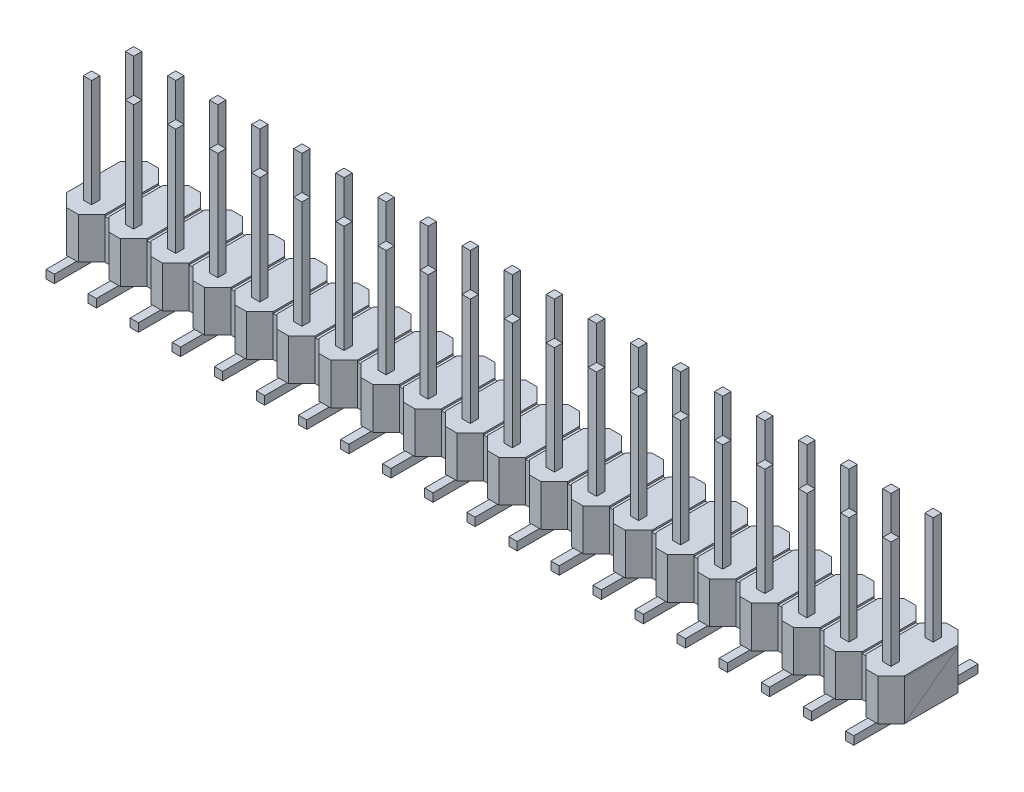
SolidWorks part; units mm, degrees
ref_plane "Alzado" through (0, 0, 0) normal (0, 0, 1) x (1, 0, 0)
ref_plane "Planta" through (0, 0, 0) normal (0, 1, 0) x (1, 0, 0)
ref_plane "Vista lateral" through (0, 0, 0) normal (1, 0, 0) x (0, 0, -1)
sketch "Croquis1" plane through (0, 0, 0) normal (0, 1, 0) x (1, 0, 0)
  line L0 (2.54, 0) -> (3.04, 0)
  line L1 (0, 0) -> (0.5, 0)
  line L2 (0, 0) -> (0, 0.5)
  line L3 (0, 0.5) -> (0.5, 0.5)
  line L4 (0.5, 0) -> (0.5, 0.5)
  line L5 (2.54, 0) -> (2.54, 0.5)
  line L6 (2.54, 0.5) -> (3.04, 0.5)
  line L7 (3.04, 0) -> (3.04, 0.5)
  line L8 (5.08, 0) -> (5.58, 0)
  line L9 (5.08, 0) -> (5.08, 0.5)
  line L10 (5.08, 0.5) -> (5.58, 0.5)
  line L11 (5.58, 0) -> (5.58, 0.5)
  line L12 (7.62, 0) -> (8.12, 0)
  line L13 (7.62, 0) -> (7.62, 0.5)
  line L14 (7.62, 0.5) -> (8.12, 0.5)
  line L15 (8.12, 0) -> (8.12, 0.5)
  line L16 (10.16, 0) -> (10.66, 0)
  line L17 (10.16, 0) -> (10.16, 0.5)
  line L18 (10.16, 0.5) -> (10.66, 0.5)
  line L19 (10.66, 0) -> (10.66, 0.5)
  line L20 (12.7, 0) -> (13.2, 0)
  line L21 (12.7, 0) -> (12.7, 0.5)
  line L22 (12.7, 0.5) -> (13.2, 0.5)
  line L23 (13.2, 0) -> (13.2, 0.5)
  line L24 (15.24, 0) -> (15.74, 0)
  line L25 (15.24, 0) -> (15.24, 0.5)
  line L26 (15.24, 0.5) -> (15.74, 0.5)
  line L27 (15.74, 0) -> (15.74, 0.5)
  line L28 (17.78, 0) -> (18.28, 0)
  line L29 (17.78, 0) -> (17.78, 0.5)
  line L30 (17.78, 0.5) -> (18.28, 0.5)
  line L31 (18.28, 0) -> (18.28, 0.5)
  line L32 (20.32, 0) -> (20.82, 0)
  line L33 (20.32, 0) -> (20.32, 0.5)
  line L34 (20.32, 0.5) -> (20.82, 0.5)
  line L35 (20.82, 0) -> (20.82, 0.5)
  line L36 (22.86, 0) -> (23.36, 0)
  line L37 (22.86, 0) -> (22.86, 0.5)
  line L38 (22.86, 0.5) -> (23.36, 0.5)
  line L39 (23.36, 0) -> (23.36, 0.5)
  line L40 (25.4, 0) -> (25.9, 0)
  line L41 (25.4, 0) -> (25.4, 0.5)
  line L42 (25.4, 0.5) -> (25.9, 0.5)
  line L43 (25.9, 0) -> (25.9, 0.5)
  line L44 (27.94, 0) -> (28.44, 0)
  line L45 (27.94, 0) -> (27.94, 0.5)
  line L46 (27.94, 0.5) -> (28.44, 0.5)
  line L47 (28.44, 0) -> (28.44, 0.5)
  line L48 (30.48, 0) -> (30.98, 0)
  line L49 (30.48, 0) -> (30.48, 0.5)
  line L50 (30.48, 0.5) -> (30.98, 0.5)
  line L51 (30.98, 0) -> (30.98, 0.5)
  line L52 (33.02, 0) -> (33.52, 0)
  line L53 (33.02, 0) -> (33.02, 0.5)
  line L54 (33.02, 0.5) -> (33.52, 0.5)
  line L55 (33.52, 0) -> (33.52, 0.5)
  line L56 (35.56, 0) -> (36.06, 0)
  line L57 (35.56, 0) -> (35.56, 0.5)
  line L58 (35.56, 0.5) -> (36.06, 0.5)
  line L59 (36.06, 0) -> (36.06, 0.5)
  line L60 (38.1, 0) -> (38.6, 0)
  line L61 (38.1, 0) -> (38.1, 0.5)
  line L62 (38.1, 0.5) -> (38.6, 0.5)
  line L63 (38.6, 0) -> (38.6, 0.5)
  line L64 (40.64, 0) -> (41.14, 0)
  line L65 (40.64, 0) -> (40.64, 0.5)
  line L66 (40.64, 0.5) -> (41.14, 0.5)
  line L67 (41.14, 0) -> (41.14, 0.5)
  line L68 (43.18, 0) -> (43.68, 0)
  line L69 (43.18, 0) -> (43.18, 0.5)
  line L70 (43.18, 0.5) -> (43.68, 0.5)
  line L71 (43.68, 0) -> (43.68, 0.5)
  line L72 (45.72, 0) -> (46.22, 0)
  line L73 (45.72, 0) -> (45.72, 0.5)
  line L74 (45.72, 0.5) -> (46.22, 0.5)
  line L75 (46.22, 0) -> (46.22, 0.5)
  line L76 (48.26, 0) -> (48.76, 0)
  line L77 (48.26, 0) -> (48.26, 0.5)
  line L78 (48.26, 0.5) -> (48.76, 0.5)
  line L79 (48.76, 0) -> (48.76, 0.5)
  line L80 (0, 2.54) -> (0.5, 2.54)
  line L81 (0, 2.54) -> (0, 3.04)
  line L82 (0, 3.04) -> (0.5, 3.04)
  line L83 (0.5, 2.54) -> (0.5, 3.04)
  line L84 (2.54, 2.54) -> (3.04, 2.54)
  line L85 (2.54, 2.54) -> (2.54, 3.04)
  line L86 (2.54, 3.04) -> (3.04, 3.04)
  line L87 (3.04, 2.54) -> (3.04, 3.04)
  line L88 (5.08, 2.54) -> (5.58, 2.54)
  line L89 (5.08, 2.54) -> (5.08, 3.04)
  line L90 (5.08, 3.04) -> (5.58, 3.04)
  line L91 (5.58, 2.54) -> (5.58, 3.04)
  line L92 (7.62, 2.54) -> (8.12, 2.54)
  line L93 (7.62, 2.54) -> (7.62, 3.04)
  line L94 (7.62, 3.04) -> (8.12, 3.04)
  line L95 (8.12, 2.54) -> (8.12, 3.04)
  line L96 (10.16, 2.54) -> (10.66, 2.54)
  line L97 (10.16, 2.54) -> (10.16, 3.04)
  line L98 (10.16, 3.04) -> (10.66, 3.04)
  line L99 (10.66, 2.54) -> (10.66, 3.04)
  line L100 (12.7, 2.54) -> (13.2, 2.54)
  line L101 (12.7, 2.54) -> (12.7, 3.04)
  line L102 (12.7, 3.04) -> (13.2, 3.04)
  line L103 (13.2, 2.54) -> (13.2, 3.04)
  line L104 (15.24, 2.54) -> (15.74, 2.54)
  line L105 (15.24, 2.54) -> (15.24, 3.04)
  line L106 (15.24, 3.04) -> (15.74, 3.04)
  line L107 (15.74, 2.54) -> (15.74, 3.04)
  line L108 (17.78, 2.54) -> (18.28, 2.54)
  line L109 (17.78, 2.54) -> (17.78, 3.04)
  line L110 (17.78, 3.04) -> (18.28, 3.04)
  line L111 (18.28, 2.54) -> (18.28, 3.04)
  line L112 (20.32, 2.54) -> (20.82, 2.54)
  line L113 (20.32, 2.54) -> (20.32, 3.04)
  line L114 (20.32, 3.04) -> (20.82, 3.04)
  line L115 (20.82, 2.54) -> (20.82, 3.04)
  line L116 (22.86, 2.54) -> (23.36, 2.54)
  line L117 (22.86, 2.54) -> (22.86, 3.04)
  line L118 (22.86, 3.04) -> (23.36, 3.04)
  line L119 (23.36, 2.54) -> (23.36, 3.04)
  line L120 (25.4, 2.54) -> (25.9, 2.54)
  line L121 (25.4, 2.54) -> (25.4, 3.04)
  line L122 (25.4, 3.04) -> (25.9, 3.04)
  line L123 (25.9, 2.54) -> (25.9, 3.04)
  line L124 (27.94, 2.54) -> (28.44, 2.54)
  line L125 (27.94, 2.54) -> (27.94, 3.04)
  line L126 (27.94, 3.04) -> (28.44, 3.04)
  line L127 (28.44, 2.54) -> (28.44, 3.04)
  line L128 (30.48, 2.54) -> (30.98, 2.54)
  line L129 (30.48, 2.54) -> (30.48, 3.04)
  line L130 (30.48, 3.04) -> (30.98, 3.04)
  line L131 (30.98, 2.54) -> (30.98, 3.04)
  line L132 (33.02, 2.54) -> (33.52, 2.54)
  line L133 (33.02, 2.54) -> (33.02, 3.04)
  line L134 (33.02, 3.04) -> (33.52, 3.04)
  line L135 (33.52, 2.54) -> (33.52, 3.04)
  line L136 (35.56, 2.54) -> (36.06, 2.54)
  line L137 (35.56, 2.54) -> (35.56, 3.04)
  line L138 (35.56, 3.04) -> (36.06, 3.04)
  line L139 (36.06, 2.54) -> (36.06, 3.04)
  line L140 (38.1, 2.54) -> (38.6, 2.54)
  line L141 (38.1, 2.54) -> (38.1, 3.04)
  line L142 (38.1, 3.04) -> (38.6, 3.04)
  line L143 (38.6, 2.54) -> (38.6, 3.04)
  line L144 (40.64, 2.54) -> (41.14, 2.54)
  line L145 (40.64, 2.54) -> (40.64, 3.04)
  line L146 (40.64, 3.04) -> (41.14, 3.04)
  line L147 (41.14, 2.54) -> (41.14, 3.04)
  line L148 (43.18, 2.54) -> (43.68, 2.54)
  line L149 (43.18, 2.54) -> (43.18, 3.04)
  line L150 (43.18, 3.04) -> (43.68, 3.04)
  line L151 (43.68, 2.54) -> (43.68, 3.04)
  line L152 (45.72, 2.54) -> (46.22, 2.54)
  line L153 (45.72, 2.54) -> (45.72, 3.04)
  line L154 (45.72, 3.04) -> (46.22, 3.04)
  line L155 (46.22, 2.54) -> (46.22, 3.04)
  line L156 (48.26, 2.54) -> (48.76, 2.54)
  line L157 (48.26, 2.54) -> (48.26, 3.04)
  line L158 (48.26, 3.04) -> (48.76, 3.04)
  line L159 (48.76, 2.54) -> (48.76, 3.04)
  line L160 (0, 0) -> (2.54, 0) construction
  line L161 (0, 0) -> (0, 2.54) construction
  dimension "D1" = 0.5
  dimension "D2" = 0.5
  dimension "D3" = 90
  dimension "D4" = 2.54
  dimension "D5" = 2.54
extrude "Extruir1" add sketch "Croquis1" along normal blind 9.5
sketch "Croquis2" plane through (0, 0, 0) normal (0, -1, 0) x (1, 0, 0)
  line L0 (2.54, 2.25) -> (3.04, 2.25)
  line L1 (0, 2.25) -> (0.5, 2.25)
  line L2 (0, 2.25) -> (0, -5.25)
  line L3 (0, -5.25) -> (0.5, -5.25)
  line L4 (0.5, 2.25) -> (0.5, -5.25)
  line L5 (2.54, 2.25) -> (2.54, -5.25)
  line L6 (2.54, -5.25) -> (3.04, -5.25)
  line L7 (3.04, 2.25) -> (3.04, -5.25)
  line L8 (5.08, 2.25) -> (5.58, 2.25)
  line L9 (5.08, 2.25) -> (5.08, -5.25)
  line L10 (5.08, -5.25) -> (5.58, -5.25)
  line L11 (5.58, 2.25) -> (5.58, -5.25)
  line L12 (7.62, 2.25) -> (8.12, 2.25)
  line L13 (7.62, 2.25) -> (7.62, -5.25)
  line L14 (7.62, -5.25) -> (8.12, -5.25)
  line L15 (8.12, 2.25) -> (8.12, -5.25)
  line L16 (10.16, 2.25) -> (10.66, 2.25)
  line L17 (10.16, 2.25) -> (10.16, -5.25)
  line L18 (10.16, -5.25) -> (10.66, -5.25)
  line L19 (10.66, 2.25) -> (10.66, -5.25)
  line L20 (12.7, 2.25) -> (13.2, 2.25)
  line L21 (12.7, 2.25) -> (12.7, -5.25)
  line L22 (12.7, -5.25) -> (13.2, -5.25)
  line L23 (13.2, 2.25) -> (13.2, -5.25)
  line L24 (15.24, 2.25) -> (15.74, 2.25)
  line L25 (15.24, 2.25) -> (15.24, -5.25)
  line L26 (15.24, -5.25) -> (15.74, -5.25)
  line L27 (15.74, 2.25) -> (15.74, -5.25)
  line L28 (17.78, 2.25) -> (18.28, 2.25)
  line L29 (17.78, 2.25) -> (17.78, -5.25)
  line L30 (17.78, -5.25) -> (18.28, -5.25)
  line L31 (18.28, 2.25) -> (18.28, -5.25)
  line L32 (20.32, 2.25) -> (20.82, 2.25)
  line L33 (20.32, 2.25) -> (20.32, -5.25)
  line L34 (20.32, -5.25) -> (20.82, -5.25)
  line L35 (20.82, 2.25) -> (20.82, -5.25)
  line L36 (22.86, 2.25) -> (23.36, 2.25)
  line L37 (22.86, 2.25) -> (22.86, -5.25)
  line L38 (22.86, -5.25) -> (23.36, -5.25)
  line L39 (23.36, 2.25) -> (23.36, -5.25)
  line L40 (25.4, 2.25) -> (25.9, 2.25)
  line L41 (25.4, 2.25) -> (25.4, -5.25)
  line L42 (25.4, -5.25) -> (25.9, -5.25)
  line L43 (25.9, 2.25) -> (25.9, -5.25)
  line L44 (27.94, 2.25) -> (28.44, 2.25)
  line L45 (27.94, 2.25) -> (27.94, -5.25)
  line L46 (27.94, -5.25) -> (28.44, -5.25)
  line L47 (28.44, 2.25) -> (28.44, -5.25)
  line L48 (30.48, 2.25) -> (30.98, 2.25)
  line L49 (30.48, 2.25) -> (30.48, -5.25)
  line L50 (30.48, -5.25) -> (30.98, -5.25)
  line L51 (30.98, 2.25) -> (30.98, -5.25)
  line L52 (33.02, 2.25) -> (33.52, 2.25)
  line L53 (33.02, 2.25) -> (33.02, -5.25)
  line L54 (33.02, -5.25) -> (33.52, -5.25)
  line L55 (33.52, 2.25) -> (33.52, -5.25)
  line L56 (35.56, 2.25) -> (36.06, 2.25)
  line L57 (35.56, 2.25) -> (35.56, -5.25)
  line L58 (35.56, -5.25) -> (36.06, -5.25)
  line L59 (36.06, 2.25) -> (36.06, -5.25)
  line L60 (38.1, 2.25) -> (38.6, 2.25)
  line L61 (38.1, 2.25) -> (38.1, -5.25)
  line L62 (38.1, -5.25) -> (38.6, -5.25)
  line L63 (38.6, 2.25) -> (38.6, -5.25)
  line L64 (40.64, 2.25) -> (41.14, 2.25)
  line L65 (40.64, 2.25) -> (40.64, -5.25)
  line L66 (40.64, -5.25) -> (41.14, -5.25)
  line L67 (41.14, 2.25) -> (41.14, -5.25)
  line L68 (43.18, 2.25) -> (43.68, 2.25)
  line L69 (43.18, 2.25) -> (43.18, -5.25)
  line L70 (43.18, -5.25) -> (43.68, -5.25)
  line L71 (43.68, 2.25) -> (43.68, -5.25)
  line L72 (45.72, 2.25) -> (46.22, 2.25)
  line L73 (45.72, 2.25) -> (45.72, -5.25)
  line L74 (45.72, -5.25) -> (46.22, -5.25)
  line L75 (46.22, 2.25) -> (46.22, -5.25)
  line L76 (48.26, 2.25) -> (48.76, 2.25)
  line L77 (48.26, 2.25) -> (48.26, -5.25)
  line L78 (48.26, -5.25) -> (48.76, -5.25)
  line L79 (48.76, 2.25) -> (48.76, -5.25)
  dimension "D1" = 7.5
  dimension "D2" = 0.5
  dimension "D3" = 2.25
  dimension "D4" = 2.54
extrude "Extruir2" add sketch "Croquis2" against normal blind 0.5
sketch "Croquis3" plane through (0, 0.5, 0) normal (0, 1, 0) x (-1, 0, 0)
  line L0 (-0.5, -5.25) -> (-0.5, -3.04) construction
  line L1 (-0.6, -3.94) -> (0.1, -3.94)
  line L2 (-1.4, -3.14) -> (-1.4, 0.1)
  line L3 (-0.6, 0.9) -> (0.1, 0.9)
  line L4 (0.9, -3.14) -> (0.9, 0.1)
  line L5 (0, -3.04) -> (0, -5.25) construction
  line L6 (-0.5, -3.04) -> (0, -3.04) construction
  line L7 (-0.5, 0) -> (0, 0) construction
  line L8 (-1.4, -3.14) -> (-0.6, -3.94)
  line L9 (0.1, -3.94) -> (0.9, -3.14)
  line L10 (0.1, 0.9) -> (0.9, 0.1)
  line L11 (-1.4, 0.1) -> (-0.6, 0.9)
  line L12 (-3.14, -3.94) -> (-2.44, -3.94)
  line L13 (-3.94, -3.14) -> (-3.94, 0.1)
  line L14 (-3.14, 0.9) -> (-2.44, 0.9)
  line L15 (-1.64, -3.14) -> (-1.64, 0.1)
  line L16 (-3.94, -3.14) -> (-3.14, -3.94)
  line L17 (-2.44, -3.94) -> (-1.64, -3.14)
  line L18 (-2.44, 0.9) -> (-1.64, 0.1)
  line L19 (-3.94, 0.1) -> (-3.14, 0.9)
  line L20 (-5.68, -3.94) -> (-4.98, -3.94)
  line L21 (-6.48, -3.14) -> (-6.48, 0.1)
  line L22 (-5.68, 0.9) -> (-4.98, 0.9)
  line L23 (-4.18, -3.14) -> (-4.18, 0.1)
  line L24 (-6.48, -3.14) -> (-5.68, -3.94)
  line L25 (-4.98, -3.94) -> (-4.18, -3.14)
  line L26 (-4.98, 0.9) -> (-4.18, 0.1)
  line L27 (-6.48, 0.1) -> (-5.68, 0.9)
  line L28 (-8.22, -3.94) -> (-7.52, -3.94)
  line L29 (-9.02, -3.14) -> (-9.02, 0.1)
  line L30 (-8.22, 0.9) -> (-7.52, 0.9)
  line L31 (-6.72, -3.14) -> (-6.72, 0.1)
  line L32 (-9.02, -3.14) -> (-8.22, -3.94)
  line L33 (-7.52, -3.94) -> (-6.72, -3.14)
  line L34 (-7.52, 0.9) -> (-6.72, 0.1)
  line L35 (-9.02, 0.1) -> (-8.22, 0.9)
  line L36 (-10.76, -3.94) -> (-10.06, -3.94)
  line L37 (-11.56, -3.14) -> (-11.56, 0.1)
  line L38 (-10.76, 0.9) -> (-10.06, 0.9)
  line L39 (-9.26, -3.14) -> (-9.26, 0.1)
  line L40 (-11.56, -3.14) -> (-10.76, -3.94)
  line L41 (-10.06, -3.94) -> (-9.26, -3.14)
  line L42 (-10.06, 0.9) -> (-9.26, 0.1)
  line L43 (-11.56, 0.1) -> (-10.76, 0.9)
  line L44 (-13.3, -3.94) -> (-12.6, -3.94)
  line L45 (-14.1, -3.14) -> (-14.1, 0.1)
  line L46 (-13.3, 0.9) -> (-12.6, 0.9)
  line L47 (-11.8, -3.14) -> (-11.8, 0.1)
  line L48 (-14.1, -3.14) -> (-13.3, -3.94)
  line L49 (-12.6, -3.94) -> (-11.8, -3.14)
  line L50 (-12.6, 0.9) -> (-11.8, 0.1)
  line L51 (-14.1, 0.1) -> (-13.3, 0.9)
  line L52 (-15.84, -3.94) -> (-15.14, -3.94)
  line L53 (-16.64, -3.14) -> (-16.64, 0.1)
  line L54 (-15.84, 0.9) -> (-15.14, 0.9)
  line L55 (-14.34, -3.14) -> (-14.34, 0.1)
  line L56 (-16.64, -3.14) -> (-15.84, -3.94)
  line L57 (-15.14, -3.94) -> (-14.34, -3.14)
  line L58 (-15.14, 0.9) -> (-14.34, 0.1)
  line L59 (-16.64, 0.1) -> (-15.84, 0.9)
  line L60 (-18.38, -3.94) -> (-17.68, -3.94)
  line L61 (-19.18, -3.14) -> (-19.18, 0.1)
  line L62 (-18.38, 0.9) -> (-17.68, 0.9)
  line L63 (-16.88, -3.14) -> (-16.88, 0.1)
  line L64 (-19.18, -3.14) -> (-18.38, -3.94)
  line L65 (-17.68, -3.94) -> (-16.88, -3.14)
  line L66 (-17.68, 0.9) -> (-16.88, 0.1)
  line L67 (-19.18, 0.1) -> (-18.38, 0.9)
  line L68 (-20.92, -3.94) -> (-20.22, -3.94)
  line L69 (-21.72, -3.14) -> (-21.72, 0.1)
  line L70 (-20.92, 0.9) -> (-20.22, 0.9)
  line L71 (-19.42, -3.14) -> (-19.42, 0.1)
  line L72 (-21.72, -3.14) -> (-20.92, -3.94)
  line L73 (-20.22, -3.94) -> (-19.42, -3.14)
  line L74 (-20.22, 0.9) -> (-19.42, 0.1)
  line L75 (-21.72, 0.1) -> (-20.92, 0.9)
  line L76 (-23.46, -3.94) -> (-22.76, -3.94)
  line L77 (-24.26, -3.14) -> (-24.26, 0.1)
  line L78 (-23.46, 0.9) -> (-22.76, 0.9)
  line L79 (-21.96, -3.14) -> (-21.96, 0.1)
  line L80 (-24.26, -3.14) -> (-23.46, -3.94)
  line L81 (-22.76, -3.94) -> (-21.96, -3.14)
  line L82 (-22.76, 0.9) -> (-21.96, 0.1)
  line L83 (-24.26, 0.1) -> (-23.46, 0.9)
  line L84 (-26, -3.94) -> (-25.3, -3.94)
  line L85 (-26.8, -3.14) -> (-26.8, 0.1)
  line L86 (-26, 0.9) -> (-25.3, 0.9)
  line L87 (-24.5, -3.14) -> (-24.5, 0.1)
  line L88 (-26.8, -3.14) -> (-26, -3.94)
  line L89 (-25.3, -3.94) -> (-24.5, -3.14)
  line L90 (-25.3, 0.9) -> (-24.5, 0.1)
  line L91 (-26.8, 0.1) -> (-26, 0.9)
  line L92 (-28.54, -3.94) -> (-27.84, -3.94)
  line L93 (-29.34, -3.14) -> (-29.34, 0.1)
  line L94 (-28.54, 0.9) -> (-27.84, 0.9)
  line L95 (-27.04, -3.14) -> (-27.04, 0.1)
  line L96 (-29.34, -3.14) -> (-28.54, -3.94)
  line L97 (-27.84, -3.94) -> (-27.04, -3.14)
  line L98 (-27.84, 0.9) -> (-27.04, 0.1)
  line L99 (-29.34, 0.1) -> (-28.54, 0.9)
  line L100 (-31.08, -3.94) -> (-30.38, -3.94)
  line L101 (-31.88, -3.14) -> (-31.88, 0.1)
  line L102 (-31.08, 0.9) -> (-30.38, 0.9)
  line L103 (-29.58, -3.14) -> (-29.58, 0.1)
  line L104 (-31.88, -3.14) -> (-31.08, -3.94)
  line L105 (-30.38, -3.94) -> (-29.58, -3.14)
  line L106 (-30.38, 0.9) -> (-29.58, 0.1)
  line L107 (-31.88, 0.1) -> (-31.08, 0.9)
  line L108 (-33.62, -3.94) -> (-32.92, -3.94)
  line L109 (-34.42, -3.14) -> (-34.42, 0.1)
  line L110 (-33.62, 0.9) -> (-32.92, 0.9)
  line L111 (-32.12, -3.14) -> (-32.12, 0.1)
  line L112 (-34.42, -3.14) -> (-33.62, -3.94)
  line L113 (-32.92, -3.94) -> (-32.12, -3.14)
  line L114 (-32.92, 0.9) -> (-32.12, 0.1)
  line L115 (-34.42, 0.1) -> (-33.62, 0.9)
  line L116 (-36.16, -3.94) -> (-35.46, -3.94)
  line L117 (-36.96, -3.14) -> (-36.96, 0.1)
  line L118 (-36.16, 0.9) -> (-35.46, 0.9)
  line L119 (-34.66, -3.14) -> (-34.66, 0.1)
  line L120 (-36.96, -3.14) -> (-36.16, -3.94)
  line L121 (-35.46, -3.94) -> (-34.66, -3.14)
  line L122 (-35.46, 0.9) -> (-34.66, 0.1)
  line L123 (-36.96, 0.1) -> (-36.16, 0.9)
  line L124 (-38.7, -3.94) -> (-38, -3.94)
  line L125 (-39.5, -3.14) -> (-39.5, 0.1)
  line L126 (-38.7, 0.9) -> (-38, 0.9)
  line L127 (-37.2, -3.14) -> (-37.2, 0.1)
  line L128 (-39.5, -3.14) -> (-38.7, -3.94)
  line L129 (-38, -3.94) -> (-37.2, -3.14)
  line L130 (-38, 0.9) -> (-37.2, 0.1)
  line L131 (-39.5, 0.1) -> (-38.7, 0.9)
  line L132 (-41.24, -3.94) -> (-40.54, -3.94)
  line L133 (-42.04, -3.14) -> (-42.04, 0.1)
  line L134 (-41.24, 0.9) -> (-40.54, 0.9)
  line L135 (-39.74, -3.14) -> (-39.74, 0.1)
  line L136 (-42.04, -3.14) -> (-41.24, -3.94)
  line L137 (-40.54, -3.94) -> (-39.74, -3.14)
  line L138 (-40.54, 0.9) -> (-39.74, 0.1)
  line L139 (-42.04, 0.1) -> (-41.24, 0.9)
  line L140 (-43.78, -3.94) -> (-43.08, -3.94)
  line L141 (-44.58, -3.14) -> (-44.58, 0.1)
  line L142 (-43.78, 0.9) -> (-43.08, 0.9)
  line L143 (-42.28, -3.14) -> (-42.28, 0.1)
  line L144 (-44.58, -3.14) -> (-43.78, -3.94)
  line L145 (-43.08, -3.94) -> (-42.28, -3.14)
  line L146 (-43.08, 0.9) -> (-42.28, 0.1)
  line L147 (-44.58, 0.1) -> (-43.78, 0.9)
  line L148 (-46.32, -3.94) -> (-45.62, -3.94)
  line L149 (-47.12, -3.14) -> (-47.12, 0.1)
  line L150 (-46.32, 0.9) -> (-45.62, 0.9)
  line L151 (-44.82, -3.14) -> (-44.82, 0.1)
  line L152 (-47.12, -3.14) -> (-46.32, -3.94)
  line L153 (-45.62, -3.94) -> (-44.82, -3.14)
  line L154 (-45.62, 0.9) -> (-44.82, 0.1)
  line L155 (-47.12, 0.1) -> (-46.32, 0.9)
  line L156 (-48.86, -3.94) -> (-48.16, -3.94)
  line L157 (-49.66, -3.14) -> (-49.66, 0.1)
  line L158 (-48.86, 0.9) -> (-48.16, 0.9)
  line L159 (-47.36, -3.14) -> (-47.36, 0.1)
  line L160 (-49.66, -3.14) -> (-48.86, -3.94)
  line L161 (-48.16, -3.94) -> (-47.36, -3.14)
  line L162 (-48.16, 0.9) -> (-47.36, 0.1)
  line L163 (-49.66, 0.1) -> (-48.86, 0.9)
  line L164 (-3.04, -3.04) -> (-2.54, -3.04)
  line L165 (-0.5, -3.04) -> (0, -3.04)
  line L166 (-0.5, -3.04) -> (-0.5, -2.54)
  line L167 (-0.5, -2.54) -> (0, -2.54)
  line L168 (0, -3.04) -> (0, -2.54)
  line L169 (-0.5, -0.5) -> (0, -0.5)
  line L170 (-0.5, -0.5) -> (-0.5, 0)
  line L171 (-0.5, 0) -> (0, 0)
  line L172 (0, -0.5) -> (0, 0)
  line L173 (-3.04, -3.04) -> (-3.04, -2.54)
  line L174 (-3.04, -2.54) -> (-2.54, -2.54)
  line L175 (-2.54, -3.04) -> (-2.54, -2.54)
  line L176 (-3.04, -0.5) -> (-2.54, -0.5)
  line L177 (-3.04, -0.5) -> (-3.04, 0)
  line L178 (-3.04, 0) -> (-2.54, 0)
  line L179 (-2.54, -0.5) -> (-2.54, 0)
  line L180 (-5.58, -3.04) -> (-5.08, -3.04)
  line L181 (-5.58, -3.04) -> (-5.58, -2.54)
  line L182 (-5.58, -2.54) -> (-5.08, -2.54)
  line L183 (-5.08, -3.04) -> (-5.08, -2.54)
  line L184 (-5.58, -0.5) -> (-5.08, -0.5)
  line L185 (-5.58, -0.5) -> (-5.58, 0)
  line L186 (-5.58, 0) -> (-5.08, 0)
  line L187 (-5.08, -0.5) -> (-5.08, 0)
  line L188 (-8.12, -3.04) -> (-7.62, -3.04)
  line L189 (-8.12, -3.04) -> (-8.12, -2.54)
  line L190 (-8.12, -2.54) -> (-7.62, -2.54)
  line L191 (-7.62, -3.04) -> (-7.62, -2.54)
  line L192 (-8.12, -0.5) -> (-7.62, -0.5)
  line L193 (-8.12, -0.5) -> (-8.12, 0)
  line L194 (-8.12, 0) -> (-7.62, 0)
  line L195 (-7.62, -0.5) -> (-7.62, 0)
  line L196 (-10.66, -3.04) -> (-10.16, -3.04)
  line L197 (-10.66, -3.04) -> (-10.66, -2.54)
  line L198 (-10.66, -2.54) -> (-10.16, -2.54)
  line L199 (-10.16, -3.04) -> (-10.16, -2.54)
  line L200 (-10.66, -0.5) -> (-10.16, -0.5)
  line L201 (-10.66, -0.5) -> (-10.66, 0)
  line L202 (-10.66, 0) -> (-10.16, 0)
  line L203 (-10.16, -0.5) -> (-10.16, 0)
  line L204 (-13.2, -3.04) -> (-12.7, -3.04)
  line L205 (-13.2, -3.04) -> (-13.2, -2.54)
  line L206 (-13.2, -2.54) -> (-12.7, -2.54)
  line L207 (-12.7, -3.04) -> (-12.7, -2.54)
  line L208 (-13.2, -0.5) -> (-12.7, -0.5)
  line L209 (-13.2, -0.5) -> (-13.2, 0)
  line L210 (-13.2, 0) -> (-12.7, 0)
  line L211 (-12.7, -0.5) -> (-12.7, 0)
  line L212 (-15.74, -3.04) -> (-15.24, -3.04)
  line L213 (-15.74, -3.04) -> (-15.74, -2.54)
  line L214 (-15.74, -2.54) -> (-15.24, -2.54)
  line L215 (-15.24, -3.04) -> (-15.24, -2.54)
  line L216 (-15.74, -0.5) -> (-15.24, -0.5)
  line L217 (-15.74, -0.5) -> (-15.74, 0)
  line L218 (-15.74, 0) -> (-15.24, 0)
  line L219 (-15.24, -0.5) -> (-15.24, 0)
  line L220 (-18.28, -3.04) -> (-17.78, -3.04)
  line L221 (-18.28, -3.04) -> (-18.28, -2.54)
  line L222 (-18.28, -2.54) -> (-17.78, -2.54)
  line L223 (-17.78, -3.04) -> (-17.78, -2.54)
  line L224 (-18.28, -0.5) -> (-17.78, -0.5)
  line L225 (-18.28, -0.5) -> (-18.28, 0)
  line L226 (-18.28, 0) -> (-17.78, 0)
  line L227 (-17.78, -0.5) -> (-17.78, 0)
  line L228 (-20.82, -3.04) -> (-20.32, -3.04)
  line L229 (-20.82, -3.04) -> (-20.82, -2.54)
  line L230 (-20.82, -2.54) -> (-20.32, -2.54)
  line L231 (-20.32, -3.04) -> (-20.32, -2.54)
  line L232 (-20.82, -0.5) -> (-20.32, -0.5)
  line L233 (-20.82, -0.5) -> (-20.82, 0)
  line L234 (-20.82, 0) -> (-20.32, 0)
  line L235 (-20.32, -0.5) -> (-20.32, 0)
  line L236 (-23.36, -3.04) -> (-22.86, -3.04)
  line L237 (-23.36, -3.04) -> (-23.36, -2.54)
  line L238 (-23.36, -2.54) -> (-22.86, -2.54)
  line L239 (-22.86, -3.04) -> (-22.86, -2.54)
  line L240 (-23.36, -0.5) -> (-22.86, -0.5)
  line L241 (-23.36, -0.5) -> (-23.36, 0)
  line L242 (-23.36, 0) -> (-22.86, 0)
  line L243 (-22.86, -0.5) -> (-22.86, 0)
  line L244 (-25.9, -3.04) -> (-25.4, -3.04)
  line L245 (-25.9, -3.04) -> (-25.9, -2.54)
  line L246 (-25.9, -2.54) -> (-25.4, -2.54)
  line L247 (-25.4, -3.04) -> (-25.4, -2.54)
  line L248 (-25.9, -0.5) -> (-25.4, -0.5)
  line L249 (-25.9, -0.5) -> (-25.9, 0)
  line L250 (-25.9, 0) -> (-25.4, 0)
  line L251 (-25.4, -0.5) -> (-25.4, 0)
  line L252 (-28.44, -3.04) -> (-27.94, -3.04)
  line L253 (-28.44, -3.04) -> (-28.44, -2.54)
  line L254 (-28.44, -2.54) -> (-27.94, -2.54)
  line L255 (-27.94, -3.04) -> (-27.94, -2.54)
  line L256 (-28.44, -0.5) -> (-27.94, -0.5)
  line L257 (-28.44, -0.5) -> (-28.44, 0)
  line L258 (-28.44, 0) -> (-27.94, 0)
  line L259 (-27.94, -0.5) -> (-27.94, 0)
  line L260 (-30.98, -3.04) -> (-30.48, -3.04)
  line L261 (-30.98, -3.04) -> (-30.98, -2.54)
  line L262 (-30.98, -2.54) -> (-30.48, -2.54)
  line L263 (-30.48, -3.04) -> (-30.48, -2.54)
  line L264 (-30.98, -0.5) -> (-30.48, -0.5)
  line L265 (-30.98, -0.5) -> (-30.98, 0)
  line L266 (-30.98, 0) -> (-30.48, 0)
  line L267 (-30.48, -0.5) -> (-30.48, 0)
  line L268 (-33.52, -3.04) -> (-33.02, -3.04)
  line L269 (-33.52, -3.04) -> (-33.52, -2.54)
  line L270 (-33.52, -2.54) -> (-33.02, -2.54)
  line L271 (-33.02, -3.04) -> (-33.02, -2.54)
  line L272 (-33.52, -0.5) -> (-33.02, -0.5)
  line L273 (-33.52, -0.5) -> (-33.52, 0)
  line L274 (-33.52, 0) -> (-33.02, 0)
  line L275 (-33.02, -0.5) -> (-33.02, 0)
  line L276 (-36.06, -3.04) -> (-35.56, -3.04)
  line L277 (-36.06, -3.04) -> (-36.06, -2.54)
  line L278 (-36.06, -2.54) -> (-35.56, -2.54)
  line L279 (-35.56, -3.04) -> (-35.56, -2.54)
  line L280 (-36.06, -0.5) -> (-35.56, -0.5)
  line L281 (-36.06, -0.5) -> (-36.06, 0)
  line L282 (-36.06, 0) -> (-35.56, 0)
  line L283 (-35.56, -0.5) -> (-35.56, 0)
  line L284 (-38.6, -3.04) -> (-38.1, -3.04)
  line L285 (-38.6, -3.04) -> (-38.6, -2.54)
  line L286 (-38.6, -2.54) -> (-38.1, -2.54)
  line L287 (-38.1, -3.04) -> (-38.1, -2.54)
  line L288 (-38.6, -0.5) -> (-38.1, -0.5)
  line L289 (-38.6, -0.5) -> (-38.6, 0)
  line L290 (-38.6, 0) -> (-38.1, 0)
  line L291 (-38.1, -0.5) -> (-38.1, 0)
  line L292 (-41.14, -3.04) -> (-40.64, -3.04)
  line L293 (-41.14, -3.04) -> (-41.14, -2.54)
  line L294 (-41.14, -2.54) -> (-40.64, -2.54)
  line L295 (-40.64, -3.04) -> (-40.64, -2.54)
  line L296 (-41.14, -0.5) -> (-40.64, -0.5)
  line L297 (-41.14, -0.5) -> (-41.14, 0)
  line L298 (-41.14, 0) -> (-40.64, 0)
  line L299 (-40.64, -0.5) -> (-40.64, 0)
  line L300 (-43.68, -3.04) -> (-43.18, -3.04)
  line L301 (-43.68, -3.04) -> (-43.68, -2.54)
  line L302 (-43.68, -2.54) -> (-43.18, -2.54)
  line L303 (-43.18, -3.04) -> (-43.18, -2.54)
  line L304 (-43.68, -0.5) -> (-43.18, -0.5)
  line L305 (-43.68, -0.5) -> (-43.68, 0)
  line L306 (-43.68, 0) -> (-43.18, 0)
  line L307 (-43.18, -0.5) -> (-43.18, 0)
  line L308 (-46.22, -3.04) -> (-45.72, -3.04)
  line L309 (-46.22, -3.04) -> (-46.22, -2.54)
  line L310 (-46.22, -2.54) -> (-45.72, -2.54)
  line L311 (-45.72, -3.04) -> (-45.72, -2.54)
  line L312 (-46.22, -0.5) -> (-45.72, -0.5)
  line L313 (-46.22, -0.5) -> (-46.22, 0)
  line L314 (-46.22, 0) -> (-45.72, 0)
  line L315 (-45.72, -0.5) -> (-45.72, 0)
  line L316 (-48.76, -3.04) -> (-48.26, -3.04)
  line L317 (-48.76, -3.04) -> (-48.76, -2.54)
  line L318 (-48.76, -2.54) -> (-48.26, -2.54)
  line L319 (-48.26, -3.04) -> (-48.26, -2.54)
  line L320 (-48.76, -0.5) -> (-48.26, -0.5)
  line L321 (-48.76, -0.5) -> (-48.76, 0)
  line L322 (-48.76, 0) -> (-48.26, 0)
  line L323 (-48.26, -0.5) -> (-48.26, 0)
  point P10 (-0.25, 0)
  point P15 (-1.4, -3.94)
  point P17 (0.9, -3.94)
  point P19 (0.9, 0.9)
  point P21 (-1.4, 0.9)
  point P27 (-3.94, 0.9)
  point P29 (-1.64, 0.9)
  point P31 (-1.64, -3.94)
  point P33 (-3.94, -3.94)
  point P39 (-6.48, 0.9)
  point P41 (-4.18, 0.9)
  point P43 (-4.18, -3.94)
  point P45 (-6.48, -3.94)
  point P51 (-9.02, 0.9)
  point P53 (-6.72, 0.9)
  point P55 (-6.72, -3.94)
  point P57 (-9.02, -3.94)
  point P63 (-11.56, 0.9)
  point P65 (-9.26, 0.9)
  point P67 (-9.26, -3.94)
  point P69 (-11.56, -3.94)
  point P75 (-14.1, 0.9)
  point P77 (-11.8, 0.9)
  point P79 (-11.8, -3.94)
  point P81 (-14.1, -3.94)
  point P87 (-16.64, 0.9)
  point P89 (-14.34, 0.9)
  point P91 (-14.34, -3.94)
  point P93 (-16.64, -3.94)
  point P99 (-19.18, 0.9)
  point P101 (-16.88, 0.9)
  point P103 (-16.88, -3.94)
  point P105 (-19.18, -3.94)
  point P111 (-21.72, 0.9)
  point P113 (-19.42, 0.9)
  point P115 (-19.42, -3.94)
  point P117 (-21.72, -3.94)
  point P123 (-24.26, 0.9)
  point P125 (-21.96, 0.9)
  point P127 (-21.96, -3.94)
  point P129 (-24.26, -3.94)
  point P135 (-26.8, 0.9)
  point P137 (-24.5, 0.9)
  point P139 (-24.5, -3.94)
  point P141 (-26.8, -3.94)
  point P147 (-29.34, 0.9)
  point P149 (-27.04, 0.9)
  point P151 (-27.04, -3.94)
  point P153 (-29.34, -3.94)
  point P159 (-31.88, 0.9)
  point P161 (-29.58, 0.9)
  point P163 (-29.58, -3.94)
  point P165 (-31.88, -3.94)
  point P171 (-34.42, 0.9)
  point P173 (-32.12, 0.9)
  point P175 (-32.12, -3.94)
  point P177 (-34.42, -3.94)
  point P183 (-36.96, 0.9)
  point P185 (-34.66, 0.9)
  point P187 (-34.66, -3.94)
  point P189 (-36.96, -3.94)
  point P195 (-39.5, 0.9)
  point P197 (-37.2, 0.9)
  point P199 (-37.2, -3.94)
  point P201 (-39.5, -3.94)
  point P207 (-42.04, 0.9)
  point P209 (-39.74, 0.9)
  point P211 (-39.74, -3.94)
  point P213 (-42.04, -3.94)
  point P219 (-44.58, 0.9)
  point P221 (-42.28, 0.9)
  point P223 (-42.28, -3.94)
  point P225 (-44.58, -3.94)
  point P231 (-47.12, 0.9)
  point P233 (-44.82, 0.9)
  point P235 (-44.82, -3.94)
  point P237 (-47.12, -3.94)
  point P243 (-49.66, 0.9)
  point P245 (-47.36, 0.9)
  point P247 (-47.36, -3.94)
  point P249 (-49.66, -3.94)
  dimension "D1" = 0.9
  dimension "D2" = 0.9
  dimension "D3" = 0.9
  dimension "D4" = 0.9
  dimension "D5" = 0.8
  dimension "D6" = 45
  dimension "D7" = 0.8
  dimension "D8" = 45
  dimension "D9" = 0.8
  dimension "D10" = 45
  dimension "D11" = 0.8
  dimension "D12" = 45
  dimension "D13" = 2.54
  dimension "D14" = 2.54
extrude "Extruir4" add sketch "Croquis3" along normal blind 2.5 separate body
sketch "Croquis4" plane through (0, 0.5, 0) normal (0, -1, 0) x (1, 0, 0)
  line L1 (49.66, 0.1) -> (-0.9, 0.1)
  line L2 (49.66, 0.1) -> (49.66, -3.14)
  line L3 (49.66, -3.14) -> (-0.9, -3.14)
  line L4 (-0.9, 0.1) -> (-0.9, -3.14)
extrude "Extruir5" add sketch "Croquis4" against normal blind 2.4 separate body
